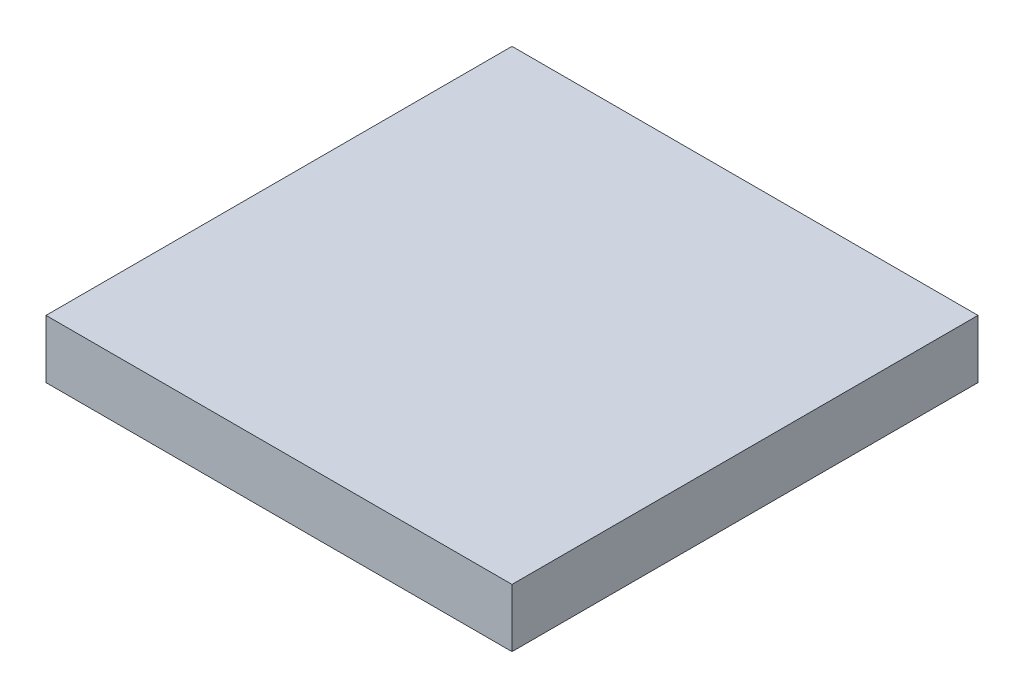
SolidWorks part; units mm, degrees
material "6061 Alloy"
ref_plane "Front Plane" through (0, 0, 0) normal (0, 0, 1) x (1, 0, 0)
ref_plane "Top Plane" through (0, 0, 0) normal (0, 1, 0) x (1, 0, 0)
ref_plane "Right Plane" through (0, 0, 0) normal (1, 0, 0) x (0, 0, -1)
sketch "Sketch1" plane through (0, 0, 0) normal (0, 1, 0) x (1, 0, 0)
  line L1 (-12.7, -12.7) -> (12.7, -12.7)
  line L2 (-12.7, -12.7) -> (-12.7, 12.7)
  line L3 (-12.7, 12.7) -> (12.7, 12.7)
  line L4 (12.7, -12.7) -> (12.7, 12.7)
  line L5 (-12.7, -12.7) -> (12.7, 12.7) construction
  line L6 (-12.7, 12.7) -> (12.7, -12.7) construction
  point P0 (0, 0)
  dimension "D1" = 25.4
  dimension "D2" = 25.4
extrude "Boss-Extrude1" add sketch "Sketch1" along normal blind 3.175
sketch "Sketch2" plane through (0, 0, 0) normal (0, -1, 0) x (1, 0, 0)
  line L1 (-11.1125, 1.5875) -> (-7.9375, 1.5875)
  line L2 (-11.1125, 1.5875) -> (-11.1125, -1.5875)
  line L3 (-11.1125, -1.5875) -> (-7.9375, -1.5875)
  line L4 (-7.9375, 1.5875) -> (-7.9375, -1.5875)
  line L5 (-11.1125, 1.5875) -> (-7.9375, -1.5875) construction
  line L6 (-11.1125, -1.5875) -> (-7.9375, 1.5875) construction
  line L14 (6.9311, 8.83) -> (4.1814, 10.4175) [skipped]
  line L15 (4.1814, 10.4175) -> (2.5939, 7.6678) [skipped]
  line L16 (5.3436, 6.0803) -> (2.5939, 7.6678) [skipped]
  line L17 (6.9311, 8.83) -> (5.3436, 6.0803) [skipped]
  line L18 (4.1814, -10.4175) -> (6.9311, -8.83) [skipped]
  line L19 (6.9311, -8.83) -> (5.3436, -6.0803) [skipped]
  line L20 (2.5939, -7.6678) -> (5.3436, -6.0803) [skipped]
  line L21 (4.1814, -10.4175) -> (2.5939, -7.6678) [skipped]
  line L30 (6.9311, 8.83) -> (4.1814, 10.4175)
  line L31 (6.9311, 8.83) -> (5.3436, 6.0803)
  line L32 (5.3436, 6.0803) -> (2.5939, 7.6678)
  line L33 (4.1814, 10.4175) -> (2.5939, 7.6678)
  line L34 (4.1814, -10.4175) -> (6.9311, -8.83)
  line L35 (4.1814, -10.4175) -> (2.5939, -7.6678)
  line L36 (2.5939, -7.6678) -> (5.3436, -6.0803)
  line L37 (6.9311, -8.83) -> (5.3436, -6.0803)
  circle A0 centre (0, 0) radius 9.525
  circle A1 centre (0, 0) radius 9.525
  circle A2 centre (0, 0) radius 9.525
  circle A3 centre (-11.1125, -1.5875) radius 0.7937
  circle A4 centre (-11.1125, 1.5875) radius 0.7937
  circle A5 centre (-7.9375, 1.5875) radius 0.7937
  circle A6 centre (-7.9375, -1.5875) radius 0.7938
  circle A15 centre (4.1814, 10.4175) radius 0.7938
  circle A16 centre (6.9311, 8.83) radius 0.7937
  circle A17 centre (5.3436, 6.0803) radius 0.7937
  circle A18 centre (2.5939, 7.6678) radius 0.7938
  circle A19 centre (6.9311, -8.83) radius 0.7937
  circle A20 centre (4.1814, -10.4175) radius 0.7937
  circle A21 centre (2.5939, -7.6678) radius 0.7938
  circle A22 centre (5.3436, -6.0803) radius 0.7938
  point P3 (-9.525, 0)
  point P21 (0, 0)
  point P29 (-9.525, 0)
  point P59 (0, 0)
  point P61 (0, 0)
  dimension "D1" = 3.175
  dimension "D4" = 1.5875
  dimension "D2" = 3.175
  dimension "D3" = 3
  dimension "D5" = 4
  dimension "D6" = 3
extrude "Cut-Extrude1" cut sketch "Sketch2" against normal blind 1.5875 contours L2 A3 L3 | L3 A3 L2 | A4 L2 A3 L3 A0 L1 | L1 A4 L2 | L2 A4 L1 | L1 A5 L4 | L4 A5 L1 | A6 L4 A5 L1 A0 L3 | L4 A6 L3 | L3 A6 L4 | A20 L34 A19 L37 A0 L35 | A22 L36 A21 L35 A0 L37 | L35 A21 L36 | L36 A21 L35 | L35 A20 L34 | L34 A20 L35 | L34 A19 L37 | L37 A19 L34 | L37 A22 L36 | L36 A22 L37 | A18 L32 A17 L31 A0 L33 | A16 L30 A15 L33 A0 L31 | L32 A17 L31 | L31 A17 L32 | L32 A18 L33 | L33 A18 L32 | L33 A15 L30 | L31 A16 L30 | L30 A16 L31 | L30 A15 L33
